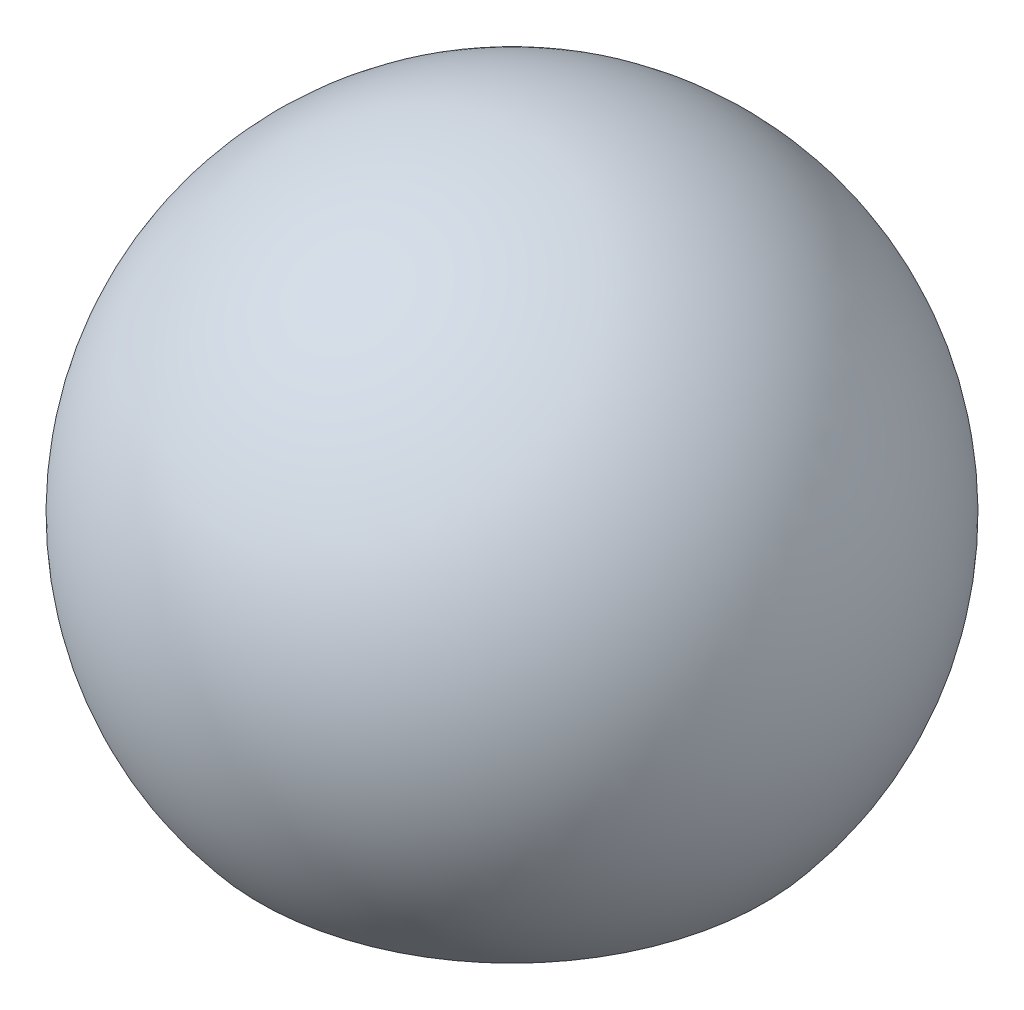
SolidWorks part; units mm, degrees
ref_plane "Front Plane" through (0, 0, 0) normal (0, 0, 1) x (1, 0, 0)
ref_plane "Top Plane" through (0, 0, 0) normal (0, 1, 0) x (1, 0, 0)
ref_plane "Right Plane" through (0, 0, 0) normal (1, 0, 0) x (0, 0, -1)
sketch "Sketch2" plane through (0, 0, 0) normal (0, 0, 1) x (1, 0, 0)
  line L0 (0, 0) -> (0, 600)
  line L1 (0, 600) -> (0, 700)
  line L2 (0, 700) -> (0, 1300)
  line L3 (0, 1300) -> (0, 2300)
  line L4 (536.2311, 150.0487) -> (1302.2756, -492.7389)
  arc A0 (0, 1300) -> (536.2311, 150.0487) centre (0, 600) cw
  arc A1 (0, 2300) -> (1302.2756, -492.7389) centre (0, 600) cw
  dimension "D4" = 1000
  dimension "D5" = 1000
  dimension "D6" = 130
revolve "Revolve1" add sketch "Sketch2" angle 360 about L2
